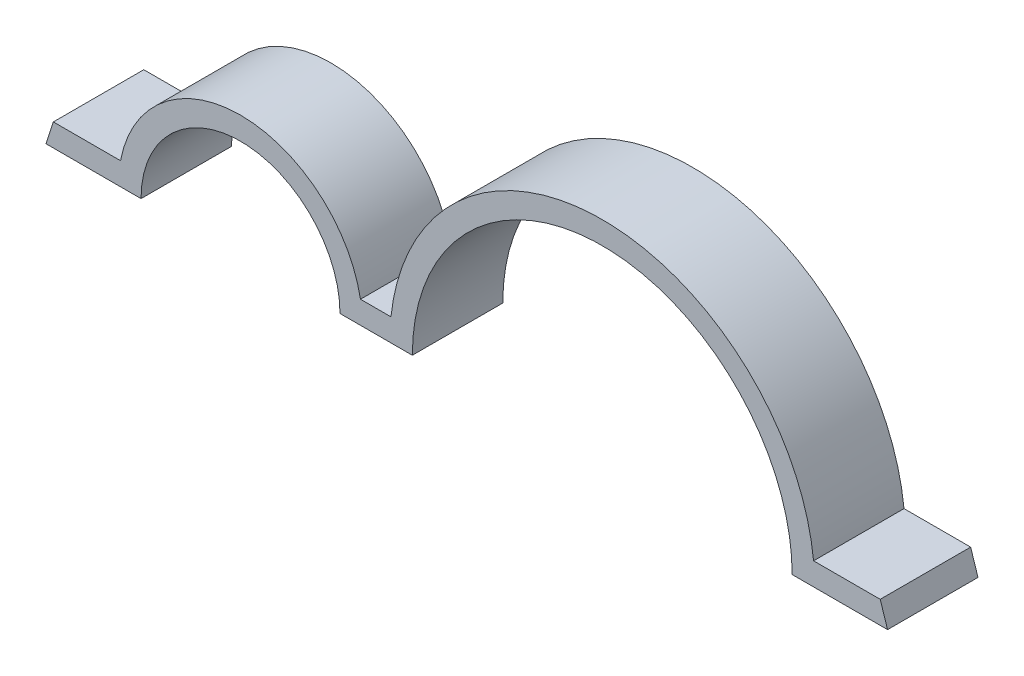
SolidWorks part; units mm, degrees
ref_plane "Front Plane" through (0, 0, 0) normal (0, 0, 1) x (1, 0, 0)
ref_plane "Top Plane" through (0, 0, 0) normal (0, 1, 0) x (1, 0, 0)
ref_plane "Right Plane" through (0, 0, 0) normal (1, 0, 0) x (0, 0, -1)
sketch "Sketch1" plane through (0, 0, 0) normal (0, 0, 1) x (1, 0, 0)
  line L0 (0, 0) -> (0, 324.652) construction
  line L1 (30.7076, 181.3003) -> (24.6961, 151.9943) construction
  line L2 (37.137, 149.4423) -> (40.6988, 166.8059) construction
  line L3 (-37.137, 149.4423) -> (-40.6988, 166.8059) construction
  line L4 (-30.7076, 181.3003) -> (-24.6961, 151.9943) construction
  line L5 (0, 0) -> (-38.8975, 189.6253) construction
  line L6 (27.6276, 178.6698) -> (37.137, 149.4423) construction
  line L7 (0, 0) -> (38.8975, 189.6253) construction
  line L12 (30.2004, 175.8931) -> (45.4337, 129.0731) construction
  line L13 (-27.6276, 178.6698) -> (-37.137, 149.4423) construction
  line L14 (-30.2004, 175.8931) -> (-45.4337, 129.0731) construction
  line L46 (-29.5452, 172.7758) -> (-22.8727, 172.7758)
  line L49 (-8.9027, 172.7758) -> (-3.8227, 172.7758)
  line L50 (22.8473, 172.7758) -> (29.5452, 172.7758)
  line L51 (-29.0287, 174.3633) -> (-24.3119, 174.3633)
  line L52 (-29.5452, 172.7758) -> (-29.0287, 174.3633)
  line L53 (29.0287, 174.3633) -> (29.5452, 172.7758)
  line L54 (24.3501, 174.3633) -> (29.0287, 174.3633)
  line L55 (-7.4635, 174.3633) -> (-5.3255, 174.3633)
  circle A0 centre (0, 0) radius 152.4 construction
  circle A1 centre (9.5123, 172.7758) radius 12.7 construction
  circle A2 centre (9.5123, 172.7758) radius 19.05 construction
  circle A3 centre (-15.8877, 172.7758) radius 6.35 construction
  circle A4 centre (-15.8877, 172.7758) radius 12.7 construction
  circle A5 centre (0, 0) radius 153.9875 construction
  circle A8 centre (0, 149.4423) radius 44.248 construction
  circle A10 centre (0, 149.4423) radius 45.8355 construction
  arc A42 (-8.9027, 172.7758) -> (-22.8727, 172.7758) centre (-15.8877, 172.7758) ccw
  arc A43 (-7.4635, 174.3633) -> (-24.3119, 174.3633) centre (-15.8877, 172.7758) ccw
  arc A44 (22.8473, 172.7758) -> (-3.8227, 172.7758) centre (9.5123, 172.7758) ccw
  arc A45 (24.3501, 174.3633) -> (-5.3255, 174.3633) centre (9.5123, 172.7758) ccw
  dimension "D1" = 304.8
  dimension "D2" = 25.4
  dimension "D3" = 1.5875
  dimension "D4" = 38.1
  dimension "D5" = 12.7
  dimension "D6" = 9.5123
  dimension "D8" = 307.975
  dimension "D11" = 88.496
  dimension "D12" = 91.671
  dimension "D13" = 1.5875
  dimension "D14" = 26.67
  dimension "D20" = 25.4
  dimension "D15" = 13.97
  dimension "D16" = 17.145
  dimension "D17" = 29.845
  dimension "D9" = 6.35
  dimension "D10" = 6.35
extrude "Boss-Extrude2" add sketch "Sketch1" along normal blind 6.35
